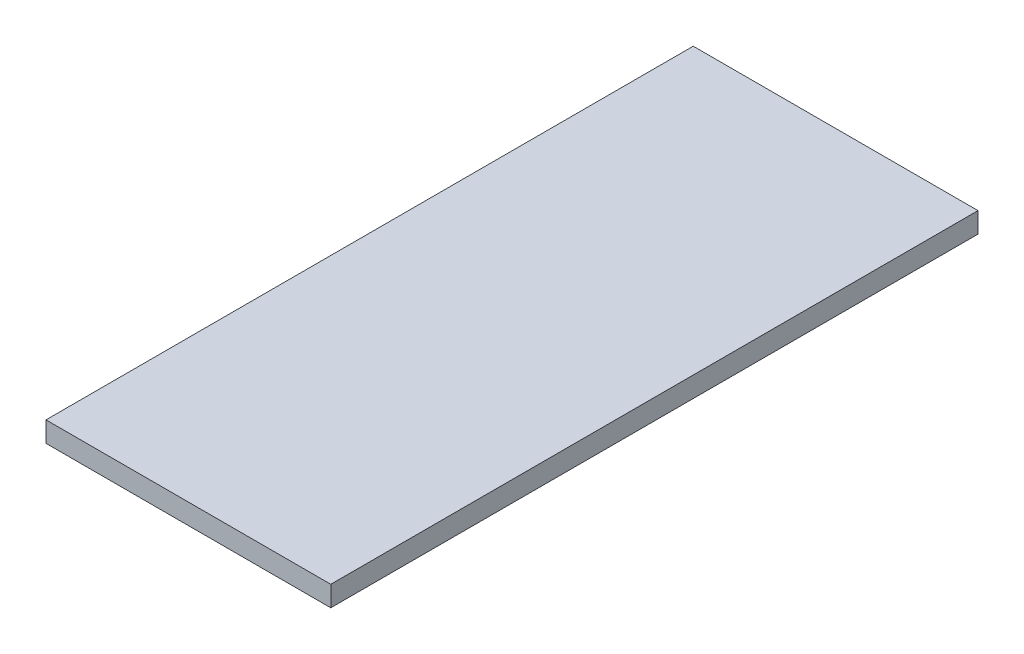
SolidWorks part; units mm, degrees
ref_plane "Front Plane" through (0, 0, 0) normal (0, 0, 1) x (1, 0, 0)
ref_plane "Top Plane" through (0, 0, 0) normal (0, 1, 0) x (1, 0, 0)
ref_plane "Right Plane" through (0, 0, 0) normal (1, 0, 0) x (0, 0, -1)
sketch "Sketch1" plane through (0, 0, 0) normal (0, 1, 0) x (1, 0, 0)
  line L1 (-11.176, -25.4) -> (11.176, -25.4)
  line L2 (-11.176, -25.4) -> (-11.176, 25.4)
  line L3 (-11.176, 25.4) -> (11.176, 25.4)
  line L4 (11.176, -25.4) -> (11.176, 25.4)
  line L5 (-11.176, -25.4) -> (11.176, 25.4) construction
  line L6 (-11.176, 25.4) -> (11.176, -25.4) construction
  point P0 (0, 0)
  dimension "D1" = 22.352
  dimension "D2" = 50.8
extrude "Boss-Extrude1" add sketch "Sketch1" along normal mid plane 1.6002
